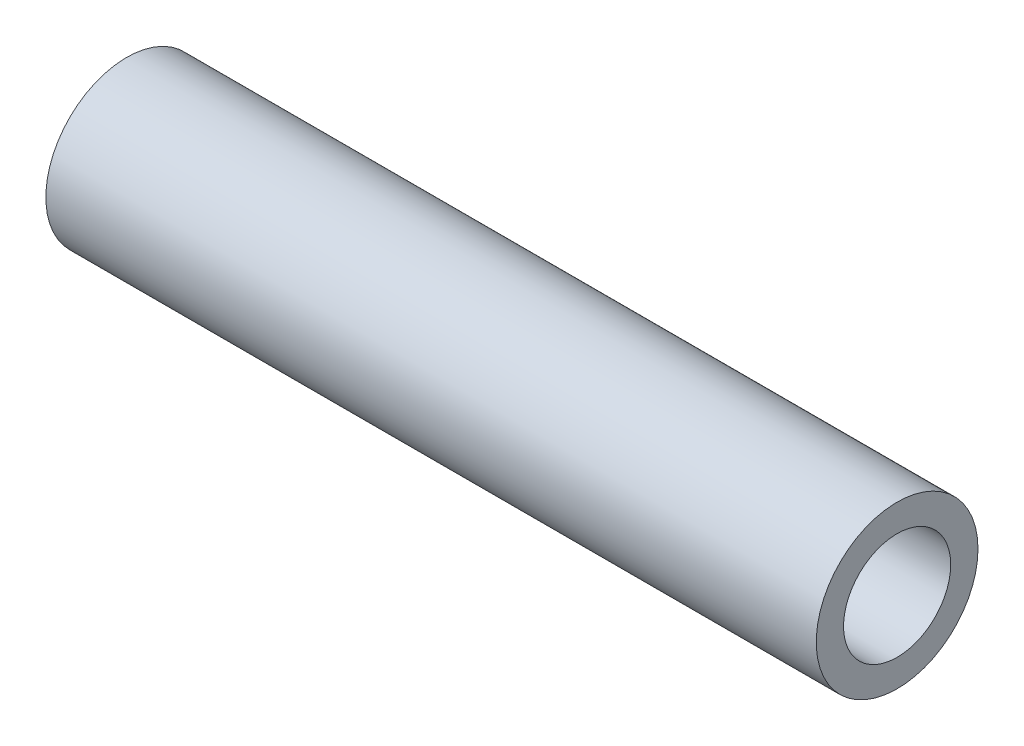
SolidWorks part; units mm, degrees
ref_plane "Front Plane" through (0, 0, 0) normal (0, 0, 1) x (1, 0, 0)
ref_plane "Top Plane" through (0, 0, 0) normal (0, 1, 0) x (1, 0, 0)
ref_plane "Right Plane" through (0, 0, 0) normal (1, 0, 0) x (0, 0, -1)
sketch "Sketch1" plane through (0, 0, 0) normal (1, 0, 0) x (0, 0, -1)
  circle A0 centre (0, 0) radius 2.65
  circle A1 centre (0, 0) radius 4
  dimension "D1" = 5.3
  dimension "D2" = 8
extrude "Boss-Extrude1" add sketch "Sketch1" along normal blind 38.1
